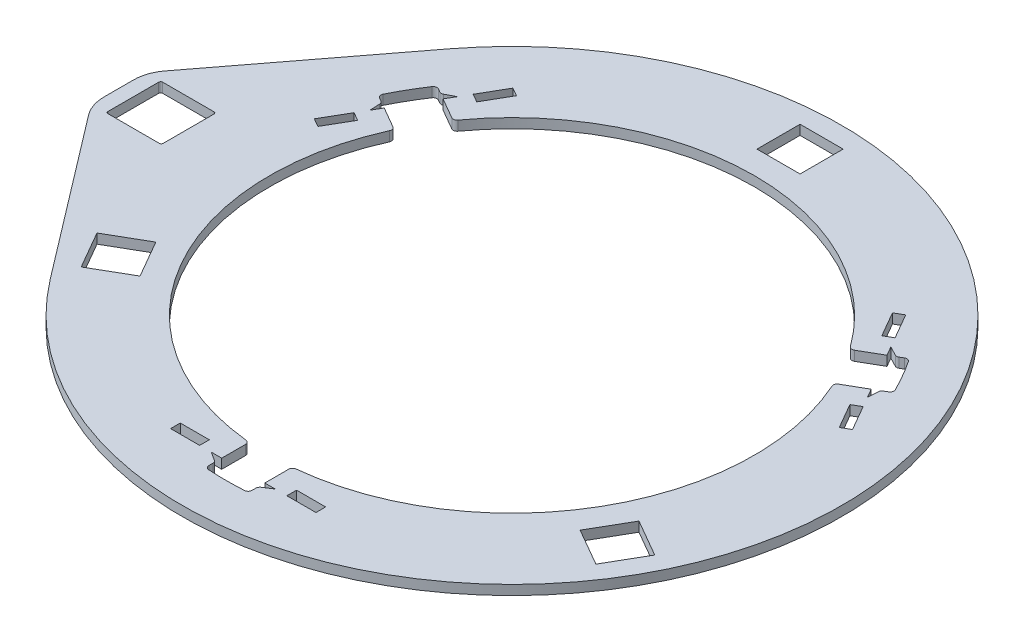
SolidWorks part; units mm, degrees
ref_plane "Front Plane" through (0, 0, 0) normal (0, 0, 1) x (1, 0, 0)
ref_plane "Top Plane" through (0, 0, 0) normal (0, 1, 0) x (1, 0, 0)
ref_plane "Right Plane" through (0, 0, 0) normal (1, 0, 0) x (0, 0, -1)
sketch "Sketch1" plane through (0, 82.4648, 0) normal (0, 1, 0) x (1, 0, 0)
  line L3 (-404.7682, 5.6751) -> (-277.6485, -161.0759)
  line L4 (-277.6485, 251.1799) -> (-404.7682, 84.4289)
  line L5 (-412.9575, 60.1786) -> (-412.9575, 29.9254)
  line L6 (-404.7682, 5.6751) -> (-277.6485, -161.0759)
  line L7 (-277.6485, 251.1799) -> (-404.7682, 84.4289)
  line L8 (-412.9575, 60.1786) -> (-412.9575, 29.9254)
  line L9 (-404.7682, 5.6751) -> (-277.6485, -161.0759)
  line L10 (-277.6485, 251.1799) -> (-404.7682, 84.4289)
  line L11 (-412.9575, 60.1786) -> (-412.9575, 29.9254)
  line L12 (-404.7682, 5.6751) -> (-277.6485, -161.0759)
  line L13 (-277.6485, 251.1799) -> (-404.7682, 84.4289)
  line L14 (-412.9575, 60.1786) -> (-412.9575, 29.9254)
  line L18 (-295.0218, -95.4256) -> (-256.527, -73.2006)
  line L19 (-397.9575, 73.252) -> (-340.9575, 73.252)
  line L20 (-397.9575, 73.252) -> (-397.9575, 16.852)
  line L21 (-397.9575, 16.852) -> (-340.9575, 16.852)
  line L22 (-340.9575, 73.252) -> (-340.9575, 16.852)
  line L23 (-295.0218, -95.4256) -> (-272.7968, -133.9204)
  line L24 (-256.527, -73.2006) -> (-234.302, -111.6954)
  line L25 (-272.7968, -133.9204) -> (-234.302, -111.6954)
  line L26 (-29.4825, 364.502) -> (-29.4825, 320.052)
  line L27 (-29.4825, 364.502) -> (14.9675, 364.502)
  line L28 (-29.4825, 320.052) -> (14.9675, 320.052)
  line L29 (14.9675, 364.502) -> (14.9675, 320.052)
  line L30 (242.012, -73.2006) -> (280.5068, -95.4256)
  line L31 (242.012, -73.2006) -> (219.787, -111.6954)
  line L32 (280.5068, -95.4256) -> (258.2818, -133.9204)
  line L33 (219.787, -111.6954) -> (258.2818, -133.9204)
  line L34 (219.787, -111.6954) -> (258.2818, -133.9204) construction
  line L35 (-272.7968, -133.9204) -> (-234.302, -111.6954) construction
  line L36 (14.9675, 320.052) -> (14.9675, 364.502) construction
  line L37 (-211.7941, 188.8045) -> (-262.2746, 217.9494)
  line L38 (-262.2746, 217.9494) -> (-284.4996, 179.4546)
  line L39 (-284.4996, 179.4546) -> (-234.0191, 150.3097)
  line L40 (197.2791, 188.8045) -> (247.7596, 217.9494)
  line L41 (247.7596, 217.9494) -> (269.9846, 179.4546)
  line L42 (269.9846, 179.4546) -> (219.5041, 150.3097)
  line L43 (-29.4825, -203.9581) -> (-29.4825, -262.248)
  line L44 (-29.4825, -262.248) -> (14.9675, -262.248)
  line L45 (14.9675, -262.248) -> (14.9675, -203.9581)
  arc A3 (-277.6485, -161.0759) -> (-277.6485, 251.1799) centre (-7.2575, 45.052) ccw
  arc A4 (-404.7682, 84.4289) -> (-412.9575, 60.1786) centre (-372.9575, 60.1786) ccw
  arc A5 (-412.9575, 29.9254) -> (-404.7682, 5.6751) centre (-372.9575, 29.9254) ccw
  arc A6 (-277.6485, -161.0759) -> (-277.6485, 251.1799) centre (-7.2575, 45.052) ccw
  arc A7 (-404.7682, 84.4289) -> (-412.9575, 60.1786) centre (-372.9575, 60.1786) ccw
  arc A8 (-412.9575, 29.9254) -> (-404.7682, 5.6751) centre (-372.9575, 29.9254) ccw
  arc A9 (-277.6485, -161.0759) -> (-277.6485, 251.1799) centre (-7.2575, 45.052) ccw
  arc A10 (-404.7682, 84.4289) -> (-412.9575, 60.1786) centre (-372.9575, 60.1786) ccw
  arc A11 (-412.9575, 29.9254) -> (-404.7682, 5.6751) centre (-372.9575, 29.9254) ccw
  arc A12 (-277.6485, -161.0759) -> (-277.6485, 251.1799) centre (-7.2575, 45.052) ccw
  arc A13 (-404.7682, 84.4289) -> (-412.9575, 60.1786) centre (-372.9575, 60.1786) ccw
  arc A14 (-412.9575, 29.9254) -> (-404.7682, 5.6751) centre (-372.9575, 29.9254) ccw
  arc A18 (14.9675, -203.9581) -> (219.5041, 150.3097) centre (-7.2575, 45.052) ccw
  arc A19 (197.2791, 188.8045) -> (-211.7941, 188.8045) centre (-7.2575, 45.052) ccw construction
  arc A20 (197.2791, 188.8045) -> (-211.7941, 188.8045) centre (-7.2575, 45.052) ccw
  arc A21 (-234.0191, 150.3097) -> (-29.4825, -203.9581) centre (-7.2575, 45.052) ccw
  dimension "D1" = 0
  dimension "D2" = 0
extrude "Boss-Extrude1" add sketch "Sketch1" against normal blind 10 contours L8 A8 L6 A6 L7 A7 A21 L39 L38 L37 A20 L40 L41 L42 A18 L45 L44 L43 L27 L29 L28 L26 L25 L23 L18 L24 L19 L22 L21 L20 L33 L31 L30 L32
sketch "Sketch5" plane through (0, 82.4648, 0) normal (0, 1, 0) x (1, 0, 0)
  line L2 (-44.4825, -232.248) -> (-29.4825, -232.248)
  line L3 (-52.2575, -232.248) -> (-29.4825, -232.248)
  line L4 (37.7425, -232.248) -> (67.7425, -232.248)
  line L5 (14.9675, -232.248) -> (37.7425, -232.248)
  line L6 (14.9675, -232.248) -> (37.7425, -232.248) construction
  line L7 (37.7425, -232.248) -> (67.7425, -232.248) construction
  line L8 (14.9675, -232.248) -> (-29.4825, -232.248) construction
  line L9 (14.9675, -239.2025) -> (25.747, -232.248)
  line L10 (14.9675, -262.248) -> (14.9675, -203.9581) construction
  line L11 (25.747, -232.248) -> (14.9675, -232.248)
  line L12 (23.9024, -232.248) -> (16.1124, -237.2738)
  line L13 (23.9024, -232.248) -> (16.1124, -237.2738) construction
  line L14 (14.9675, -232.248) -> (14.9675, -239.2025)
  line L15 (-7.2575, -262.248) -> (-7.2575, -176.0716) construction
  line L16 (-29.4825, -262.248) -> (14.9675, -262.248) construction
  line L17 (-40.2619, -232.248) -> (-29.4825, -232.248)
  line L18 (-29.4825, -232.248) -> (-29.4825, -239.2025)
  line L19 (-29.4825, -239.2025) -> (-40.2619, -232.248)
  dimension "D1" = 1
extrude "Cut-Extrude1" cut sketch "Sketch5" against normal blind 10
pattern_circular "CirPattern1" count 3 over 360 about axis through (-7.2575, 0, -45.052) along (0, 1, 0) of "Cut-Extrude1"
sketch "Sketch6" plane through (0, 82.4648, 0) normal (0, 1, 0) x (1, 0, 0)
  line L0 (-29.4825, -239.2025) -> (-29.4825, -262.248) construction
  line L4 (14.9675, -262.248) -> (14.9675, -239.2025) construction
  line L5 (-29.4825, -249.1096) -> (-29.4825, -270.3767)
  line L6 (-29.4825, -270.3767) -> (14.9675, -270.3767)
  line L7 (14.9675, -270.3767) -> (14.9675, -249.1096)
  arc A0 (-29.4825, -249.1096) -> (14.9675, -249.1096) centre (-7.2575, 45.052) ccw
  arc A1 (14.9675, -203.9581) -> (219.5041, 150.3097) centre (-7.2575, 45.052) ccw construction
  dimension "D1" = 295
extrude "Boss-Extrude2" add sketch "Sketch6" against normal blind 10
pattern_circular "CirPattern2" count 3 over 360 about axis through (-7.2575, 72.4648, -45.052) along (0, 1, 0) of "Boss-Extrude2"
sketch "Sketch7" plane through (0, 72.4648, 0) normal (0, -1, 0) x (1, 0, 0)
  line L0 (37.7425, 232.248) -> (67.7425, 232.248)
  line L1 (67.7425, 232.248) -> (67.7425, 222.248)
  line L2 (67.7425, 222.248) -> (37.7425, 222.248)
  line L3 (37.7425, 222.248) -> (37.7425, 232.248)
  line L4 (-52.2575, 232.248) -> (-52.2575, 222.248)
  line L5 (-52.2575, 222.248) -> (-82.2575, 222.248)
  line L6 (-82.2575, 222.248) -> (-82.2575, 232.248)
  line L7 (-82.2575, 232.248) -> (-52.2575, 232.248)
extrude "Cut-Extrude2" cut sketch "Sketch7" against normal blind 10
pattern_circular "CirPattern3" count 3 over 360 about axis through (-7.2575, 0, -45.052) along (0, 1, 0) of "Cut-Extrude2"
fillet "Fillet1" radius 4 18 edges at (219.5041, 77.4648, -150.3097) (197.2791, 77.4648, -188.8045) (236.3814, 77.4648, -211.3802) (258.6064, 77.4648, -172.8854) (227.8016, 77.4648, -206.4266) (250.0266, 77.4648, -167.9318) (-242.3166, 77.4648, -206.4266) (-250.8964, 77.4648, -211.3802) (-273.1214, 77.4648, -172.8854) (-264.5416, 77.4648, -167.9318) (-211.7941, 77.4648, -188.8045) (-234.0191, 77.4648, -150.3097) (-29.4825, 77.4648, 239.2025) (-29.4825, 77.4648, 249.1096) (14.9675, 77.4648, 249.1096) (14.9675, 77.4648, 239.2025) (-29.4825, 77.4648, 203.9581) (14.9675, 77.4648, 203.9581)
fillet "Fillet2" radius 2 4 edges at (-340.9575, 77.4648, -16.852) (-340.9575, 77.4648, -73.252) (-397.9575, 77.4648, -73.252) (-397.9575, 77.4648, -16.852)
